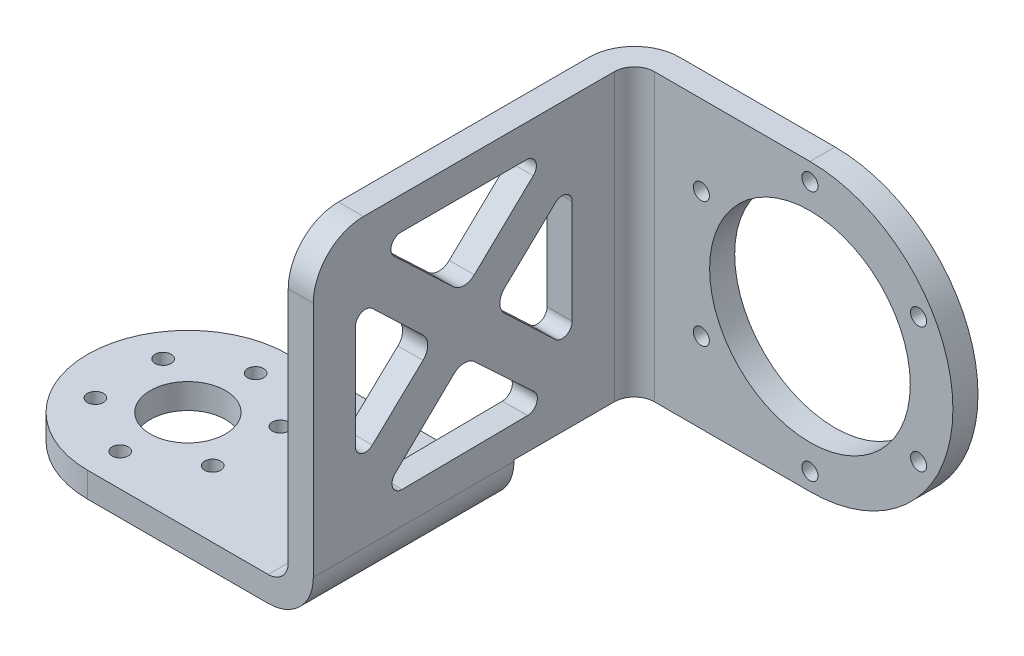
SolidWorks part; units mm, degrees
material "AISI 304"
ref_plane "前视基准面" through (0, 0, 0) normal (0, 0, 1) x (1, 0, 0)
ref_plane "上视基准面" through (0, 0, 0) normal (0, 1, 0) x (1, 0, 0)
ref_plane "右视基准面" through (0, 0, 0) normal (1, 0, 0) x (0, 0, -1)
sketch "草图1" plane through (0, 0, 0) normal (0, 1, 0) x (1, 0, 0)
  line L0 (0, 20) -> (45, 20)
  line L1 (45, 20) -> (45, -20)
  line L2 (45, -20) -> (0, -20)
  circle A0 centre (0, 0) radius 20
  dimension "D1" = 40
  dimension "D2" = 45
extrude "凸台-拉伸1" add sketch "草图1" along normal blind 5
sketch "草图3" plane through (0, 5, 0) normal (0, 1, 0) x (1, 0, 0)
  circle A0 centre (0, 0) radius 13.5 construction
  circle A1 centre (0, 13.5) radius 1.6
  circle A2 centre (11.6913, 6.75) radius 1.6
  circle A3 centre (11.6913, -6.75) radius 1.6
  circle A4 centre (0, -13.5) radius 1.6
  circle A5 centre (-11.6913, -6.75) radius 1.6
  circle A6 centre (-11.6913, 6.75) radius 1.6
  point P18 (0, 0)
  dimension "D1" = 27
  dimension "D2" = 3.2
  dimension "D3" = 6
extrude "切除-拉伸1" cut sketch "草图3" against normal blind 11
sketch "草图19" plane through (0, 0, 0) normal (0, -1, 0) x (1, 0, 0)
  circle A0 centre (0, 0) radius 7.5
  dimension "D1" = 15
sketch "草图22" plane through (45, 0, 0) normal (1, 0, 0) x (0, 0, -1)
  line L0 (20, 5) -> (-20, 5) construction
  line L1 (-20, 5) -> (20, 5)
  line L2 (-20, 5) -> (-20, 66.3)
  line L3 (-20, 66.3) -> (44, 66.3)
  line L4 (44, 9.3) -> (44, 66.3)
  line L5 (20, 5) -> (20, 9.3)
  line L6 (20, 9.3) -> (44, 9.3)
  line L7 (-20, 5) -> (-20, 0) construction
  dimension "D1" = 61.3
  dimension "D2" = 4.3
  dimension "D3" = 24
extrude "凸台-拉伸3" add sketch "草图22" against normal blind 5
sketch "草图24" plane through (0, 0, -44) normal (0, 0, -1) x (-1, 0, 0)
  line L0 (-40, 66.3) -> (-45, 66.3) construction
  line L1 (-40, 9.3) -> (-80, 9.3)
  line L2 (-40, 9.3) -> (-40, 66.3)
  line L3 (-40, 66.3) -> (-80, 66.3)
  line L4 (-40, 9.3) -> (-40, 66.3) construction
  arc A0 (-80, 66.3) -> (-80, 9.3) centre (-80, 37.8) ccw
  dimension "D1" = 57
  dimension "D2" = 40
extrude "凸台-拉伸4" add sketch "草图24" along normal blind 5
sketch "草图25" plane through (0, 0, -49) normal (0, 0, -1) x (-1, 0, 0)
  circle A0 centre (-80, 37.8) radius 20
  dimension "D1" = 40
extrude "切除-拉伸2" cut sketch "草图25" against normal blind 5
fillet "圆角1" radius 4 2 edges at (40, 5, 0) (45, 37.8, -44)
fillet "圆角4" radius 9 2 edges at (40, 37.8, -49) (45, 0, 0)
extrude "切除-拉伸3" cut sketch "草图19" against normal blind 5
sketch "草图26" plane through (0, 0, -44) normal (0, 0, 1) x (1, 0, 0)
  line L0 (105, 37.8) -> (80, 37.8) construction
  line L1 (80, 37.8) -> (101.6506, 50.3) construction
  circle A0 centre (80, 37.8) radius 25 construction
  circle A1 centre (101.6506, 50.3) radius 1.6
  circle A2 centre (101.6506, 25.3) radius 1.6
  circle A3 centre (80, 12.8) radius 1.6
  circle A4 centre (58.3494, 25.3) radius 1.6
  circle A5 centre (58.3494, 50.3) radius 1.6
  circle A6 centre (80, 62.8) radius 1.6
  point P18 (80, 37.8)
  dimension "D1" = 50
  dimension "D3" = 3.2
  dimension "D2" = 30
  dimension "D4" = 6
extrude "切除-拉伸4" cut sketch "草图26" against normal blind 5
fillet "圆角5" radius 10 1 edges at (42.5, 66.3, 20)
sketch "草图27" plane through (45, 0, 0) normal (1, 0, 0) x (0, 0, -1)
  line L13 (-17.0711, 63.3711) -> (40, 9.3) construction
  line L19 (-20, 9) -> (40, 66.3) construction
  line L20 (10.0274, 43.2072) -> (-7.5422, 59.8533)
  line L21 (-7.5422, 59.8533) -> (27.4578, 59.8533)
  line L22 (27.4578, 59.8533) -> (10.0274, 43.2072)
  line L23 (40, 66.3) -> (-10, 66.3) construction
  line L24 (15.8421, 37.6982) -> (31.6114, 52.7578)
  line L25 (31.6114, 52.7578) -> (31.6114, 22.7578)
  line L26 (31.6114, 22.7578) -> (15.8421, 37.6982)
  line L27 (40, 9.3) -> (40, 66.3) construction
  line L28 (10, 37.65) -> (40, 37.8) construction
  line L29 (10, 37.65) -> (10, 66.3) construction
  line L30 (-7.3193, 15.2724) -> (27.679, 15.6224)
  line L31 (10.083, 32.0933) -> (-7.3193, 15.2724)
  line L32 (27.679, 15.6224) -> (10.083, 32.0933)
  line L33 (-11.6114, 52.7578) -> (-11.6114, 22.7578)
  line L34 (4.1579, 37.6982) -> (-11.6114, 52.7578)
  line L35 (-11.6114, 22.7578) -> (4.1579, 37.6982)
  arc A1 (-10, 66.3) -> (-20, 56.3) centre (-10, 56.3) ccw construction
  dimension "D1" = 35
  dimension "D2" = 4
  dimension "D3" = 4
  dimension "D4" = 30
  dimension "D5" = 4
  dimension "D6" = 4
extrude "切除-拉伸5" cut sketch "草图27" against normal blind 5
fillet "圆角10" radius 2 8 edges at (42.5, 22.7578, -31.6114) (42.5, 15.2724, 7.3193) (42.5, 22.7578, 11.6114) (42.5, 15.6224, -27.679) (42.5, 52.7578, -31.6114) (42.5, 52.7578, 11.6114) (42.5, 59.8533, 7.5422) (42.5, 59.8533, -27.4578)
fillet "圆角11" radius 3 4 edges at (42.5, 37.6982, -15.8421) (42.5, 43.2072, -10.0274) (42.5, 37.6982, -4.1579) (42.5, 32.0933, -10.083)
